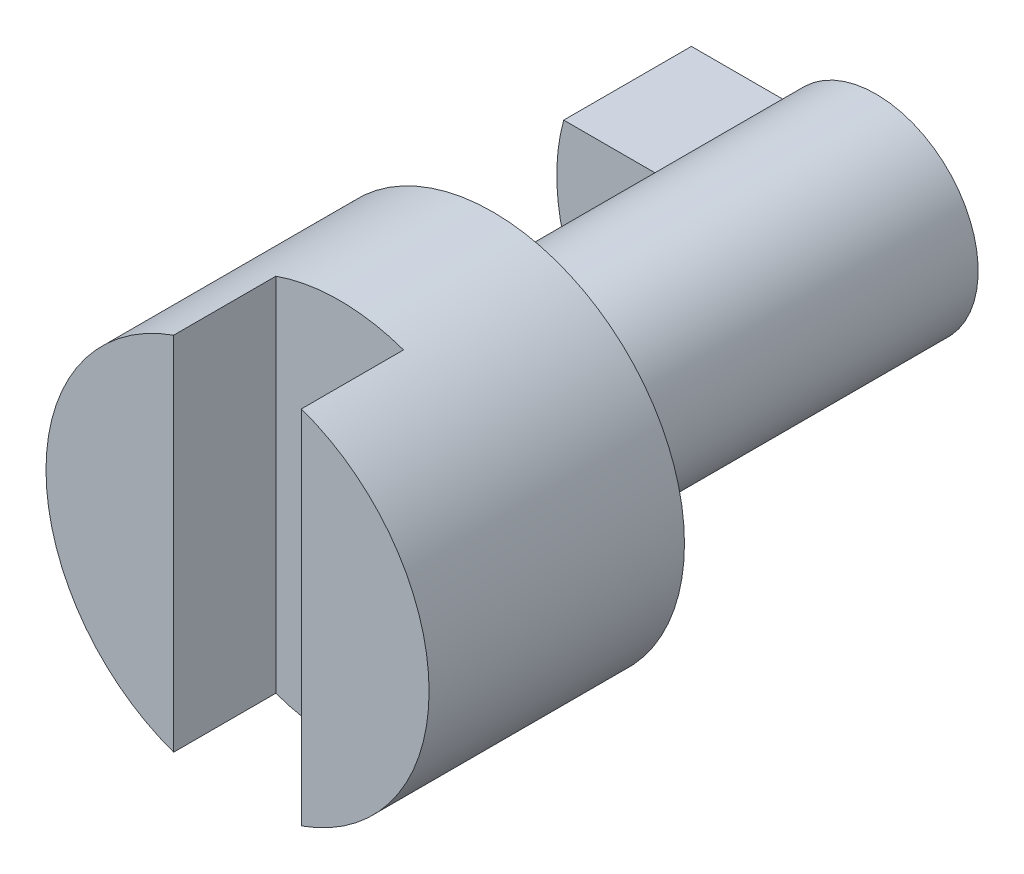
SolidWorks part; units mm, degrees
ref_plane "Front Plane" through (0, 0, 0) normal (0, 0, 1) x (1, 0, 0)
ref_plane "Top Plane" through (0, 0, 0) normal (0, 1, 0) x (1, 0, 0)
ref_plane "Right Plane" through (0, 0, 0) normal (1, 0, 0) x (0, 0, -1)
sketch "Sketch1" plane through (0, 0, 0) normal (0, 0, 1) x (1, 0, 0)
  circle A0 centre (0, 0) radius 7.5
  dimension "D1" = 15
extrude "Boss-Extrude1" add sketch "Sketch1" along normal blind 10
sketch "Sketch2" plane through (0, 0, 0) normal (0, 0, -1) x (-1, 0, 0)
  circle A0 centre (0, 0) radius 4
  dimension "D1" = 8
extrude "Boss-Extrude2" add sketch "Sketch2" along normal blind 15
sketch "Sketch3" plane through (0, 0, -15) normal (0, 0, -1) x (-1, 0, 0)
  line L0 (3.4641, 2) -> (7.2284, 2)
  line L1 (3.4641, -2) -> (7.4628, -2)
  circle A0 centre (0, 0) radius 4 construction
  circle A1 centre (0, 0) radius 7.5 construction
  arc A2 (3.4641, -2) -> (3.4641, 2) centre (0, 0) ccw
  arc A3 (7.2284, -2) -> (7.2284, 2) centre (0, 0) ccw
  circle M4 centre (0, 0) radius 4
  dimension "D1" = 4
  dimension "D2" = 2
extrude "Boss-Extrude3" add sketch "Sketch3" against normal blind 5 separate body contours L1 A3 L0 M4
sketch "Sketch4" plane through (0, 0, 10) normal (0, 0, 1) x (1, 0, 0)
  line L1 (-2.5, 35.4528) -> (2.5, 35.4528)
  line L2 (-2.5, 35.4528) -> (-2.5, -13.5654)
  line L3 (-2.5, -13.5654) -> (2.5, -13.5654)
  line L4 (2.5, 35.4528) -> (2.5, -13.5654)
  line L5 (-2.5, 35.4528) -> (2.5, -13.5654) construction
  line L6 (-2.5, -13.5654) -> (2.5, 35.4528) construction
  point P0 (0, 10.9437)
  dimension "D1" = 5
  dimension "D2" = 2.5
extrude "Cut-Extrude1" cut sketch "Sketch4" against normal blind 4
